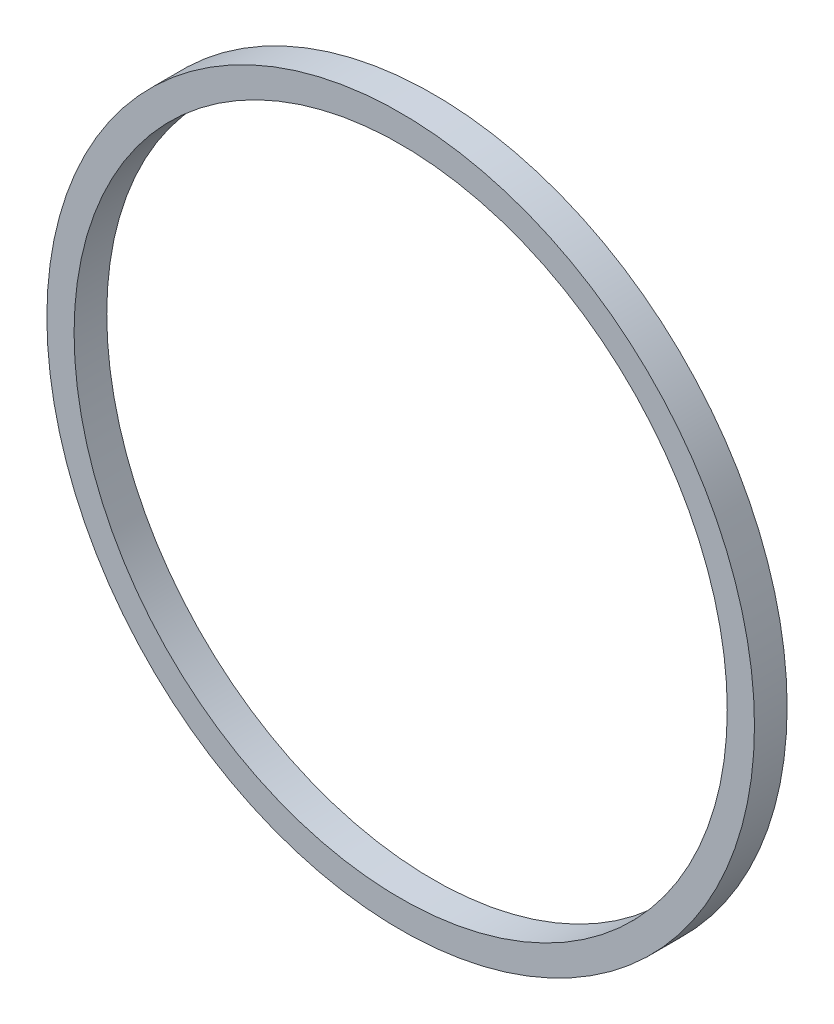
SolidWorks part; units mm, degrees
ref_plane "Front Plane" through (0, 0, 0) normal (0, 0, 1) x (1, 0, 0)
ref_plane "Top Plane" through (0, 0, 0) normal (0, 1, 0) x (1, 0, 0)
ref_plane "Right Plane" through (0, 0, 0) normal (1, 0, 0) x (0, 0, -1)
sketch "Sketch1" plane through (0, 0, 0) normal (0, 0, 1) x (1, 0, 0)
  circle A0 centre (0, 0) radius 65
  dimension "D1" = 130
extrude "Boss-Extrude1" add sketch "Sketch1" along normal blind 6
sketch "Sketch2" plane through (0, 0, 0) normal (0, 0, -1) x (-1, 0, 0)
  circle A0 centre (0, 0) radius 60
  dimension "D1" = 120
extrude "Cut-Extrude1" cut sketch "Sketch2" against normal through all
